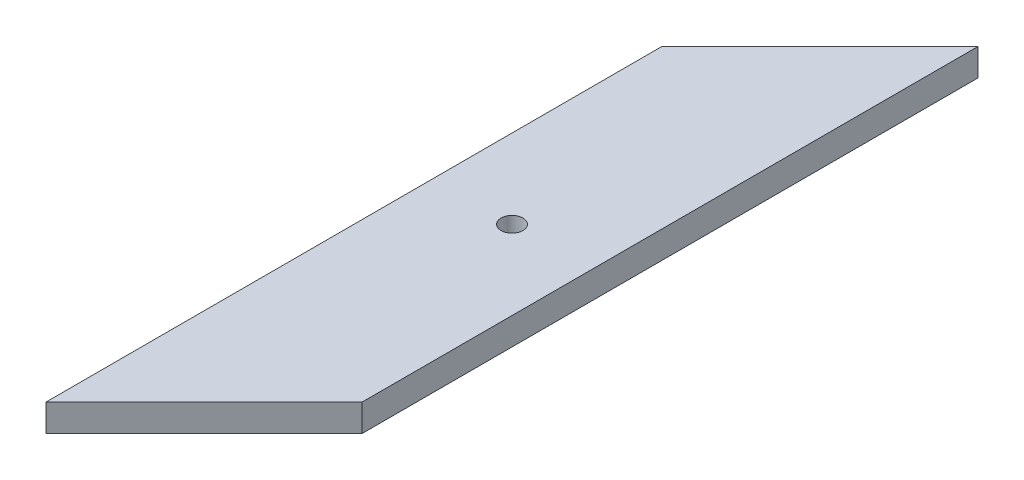
SolidWorks part; units mm, degrees
ref_plane "Front Plane" through (0, 0, 0) normal (0, 0, 1) x (1, 0, 0)
ref_plane "Top Plane" through (0, 0, 0) normal (0, 1, 0) x (1, 0, 0)
ref_plane "Right Plane" through (0, 0, 0) normal (1, 0, 0) x (0, 0, -1)
sketch "Sketch1" plane through (0, 0, 0) normal (0, 1, 0) x (1, 0, 0)
  line L0 (-62.2785, 53.6889) -> (-91.2785, 24.6889)
  line L2 (-91.2785, 24.6889) -> (-91.2785, -88.3111)
  line L4 (-62.2785, 53.6889) -> (-62.2785, -59.3111)
  line L5 (-91.2785, -88.3111) -> (-62.2785, -59.3111)
  line L6 (-76.7785, 39.1889) -> (-76.7785, -73.8111) construction
  circle A0 centre (-76.7785, -17.3111) radius 2
  dimension "D3" = 45
extrude "Boss-Extrude1" add sketch "Sketch1" along normal blind 5
